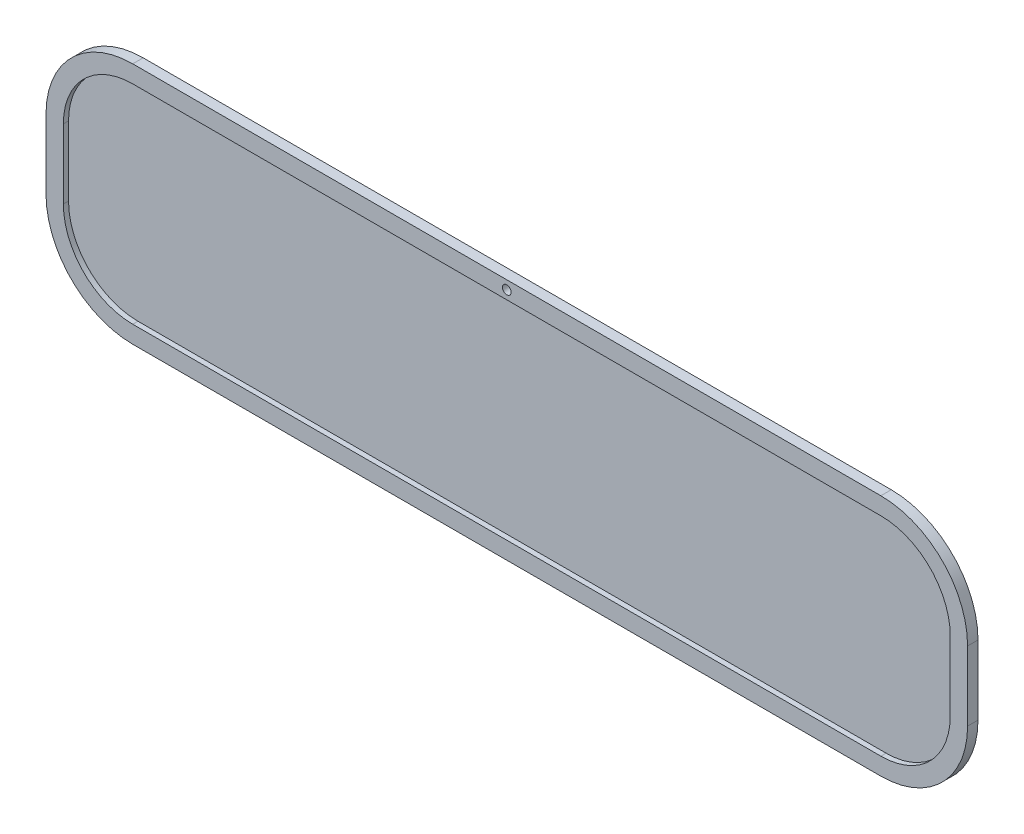
SolidWorks part; units mm, degrees
ref_plane "Ebene vorne" through (0, 0, 0) normal (0, 0, 1) x (1, 0, 0)
ref_plane "Ebene oben" through (0, 0, 0) normal (0, 1, 0) x (1, 0, 0)
ref_plane "Ebene rechts" through (0, 0, 0) normal (1, 0, 0) x (0, 0, -1)
sketch "Skizze1" plane through (0, 0, 0) normal (0, 0, 1) x (1, 0, 0)
  line L8 (432.0512, 126.1723) -> (432.0512, 206.1723)
  line L9 (432.0512, 206.1723) -> (431.4944, 212.0251)
  line L10 (431.4944, 212.0251) -> (429.8454, 217.6528)
  line L11 (429.8454, 217.6528) -> (427.1676, 222.8395)
  line L12 (427.1676, 222.8395) -> (423.5638, 227.3855)
  line L13 (423.5638, 227.3855) -> (419.1726, 231.1164)
  line L14 (419.1726, 231.1164) -> (414.1628, 233.8887)
  line L15 (414.1628, 233.8887) -> (408.7267, 235.5959)
  line L16 (408.7267, 235.5959) -> (403.0734, 236.1723)
  line L17 (403.0734, 236.1723) -> (-70.2302, 236.1723)
  line L18 (-70.2302, 236.1723) -> (-75.8835, 235.5959)
  line L19 (-75.8835, 235.5959) -> (-81.3195, 233.8887)
  line L20 (-81.3195, 233.8887) -> (-86.3294, 231.1164)
  line L21 (-86.3294, 231.1164) -> (-90.7206, 227.3855)
  line L22 (-90.7206, 227.3855) -> (-94.3243, 222.8395)
  line L23 (-94.3243, 222.8395) -> (-97.0022, 217.6528)
  line L24 (-97.0022, 217.6528) -> (-98.6512, 212.0251)
  line L25 (-98.6512, 212.0251) -> (-99.208, 206.1723)
  line L26 (-99.208, 206.1723) -> (-99.208, 126.1723)
  line L27 (-99.208, 126.1723) -> (-98.6512, 120.3196)
  line L28 (-98.6512, 120.3196) -> (-97.0022, 114.6918)
  line L29 (-97.0022, 114.6918) -> (-94.3243, 109.5052)
  line L30 (-94.3243, 109.5052) -> (-90.7206, 104.9591)
  line L31 (-90.7206, 104.9591) -> (-86.3294, 101.2283)
  line L32 (-86.3294, 101.2283) -> (-81.3195, 98.456)
  line L33 (-81.3195, 98.456) -> (-75.8835, 96.7488)
  line L34 (-75.8835, 96.7488) -> (-70.2302, 96.1723)
  line L35 (-70.2302, 96.1723) -> (403.0734, 96.1723)
  line L36 (403.0734, 96.1723) -> (408.7267, 96.7488)
  line L37 (408.7267, 96.7488) -> (414.1628, 98.456)
  line L38 (414.1628, 98.456) -> (419.1726, 101.2283)
  line L39 (419.1726, 101.2283) -> (423.5638, 104.9591)
  line L40 (423.5638, 104.9591) -> (427.1676, 109.5052)
  line L41 (427.1676, 109.5052) -> (429.8454, 114.6918)
  line L42 (429.8454, 114.6918) -> (431.4944, 120.3196)
  line L43 (431.4944, 120.3196) -> (432.0512, 126.1723)
extrude "Aufsatz-Linear austragen1" add sketch "Skizze1" along normal blind 3
sketch "Skizze2" plane through (0, 0, 0) normal (0, 0, -1) x (-1, 0, 0)
  line L0 (-403.0734, 236.1723) -> (70.2302, 236.1723) construction
  line L1 (-379.508, 96.1723) -> (-432.0512, 96.1723)
  line L2 (-379.508, 96.1723) -> (-379.508, 236.1723)
  line L3 (-379.508, 236.1723) -> (-432.0512, 236.1723)
  line L4 (-432.0512, 96.1723) -> (-432.0512, 236.1723)
  line L5 (-432.0512, 126.1723) -> (-432.0512, 206.1723) construction
  line L6 (70.2302, 96.1723) -> (-403.0734, 96.1723) construction
  line L7 (99.208, 206.1723) -> (99.208, 126.1723) construction
  line L8 (-12.0682, 236.1723) -> (99.208, 236.1723)
  line L9 (-12.0682, 236.1723) -> (-12.0682, 96.1723)
  line L10 (-12.0682, 96.1723) -> (99.208, 96.1723)
  line L11 (99.208, 236.1723) -> (99.208, 96.1723)
extrude "Aufsatz-Linear austragen2" add sketch "Skizze2" against normal blind 3
fillet "Verrundung1" radius 50 3 edges at (432.0512, 96.1723, 1.5) (-99.208, 96.1723, 1.5) (-99.208, 236.1723, 1.5)
fillet "Verrundung2" radius 50 1 edges at (432.0512, 236.1723, 1.5)
sketch "Skizze3" plane through (0, 0, 3) normal (0, 0, 1) x (1, 0, 0)
  line L0 (166.4216, 236.1723) -> (166.4216, 96.1723)
  line L1 (382.0512, 236.1723) -> (-49.208, 236.1723) construction
  line L2 (-49.208, 96.1723) -> (382.0512, 96.1723) construction
  circle A0 centre (166.4216, 231.1723) radius 2.5
  dimension "D2" = 5
  dimension "D1" = 5
extrude "Schnitt-Linear austragen1" cut sketch "Skizze3" against normal blind 10 contours A0
sketch "Skizze5" plane through (0, 0, 3) normal (0, 0, 1) x (1, 0, 0)
  line L0 (-89.208, 186.1723) -> (-89.208, 146.1723)
  line L1 (-49.208, 106.1723) -> (382.0512, 106.1723)
  line L2 (422.0512, 146.1723) -> (422.0512, 186.1723)
  line L3 (382.0512, 226.1723) -> (-49.208, 226.1723)
  line L4 (432.0512, 146.1723) -> (432.0512, 186.1723)
  line L5 (382.0512, 236.1723) -> (-49.208, 236.1723)
  line L6 (-99.208, 186.1723) -> (-99.208, 146.1723)
  line L7 (-49.208, 96.1723) -> (382.0512, 96.1723)
  line L8 (432.0512, 146.1723) -> (432.0512, 186.1723)
  line L9 (382.0512, 236.1723) -> (-49.208, 236.1723)
  line L10 (-99.208, 186.1723) -> (-99.208, 146.1723)
  line L11 (-49.208, 96.1723) -> (382.0512, 96.1723)
  arc A0 (-49.208, 226.1723) -> (-89.208, 186.1723) centre (-49.208, 186.1723) ccw
  arc A1 (-89.208, 146.1723) -> (-49.208, 106.1723) centre (-49.208, 146.1723) ccw
  arc A2 (382.0512, 106.1723) -> (422.0512, 146.1723) centre (382.0512, 146.1723) ccw
  arc A3 (422.0512, 186.1723) -> (382.0512, 226.1723) centre (382.0512, 186.1723) ccw
  arc A4 (432.0512, 186.1723) -> (382.0512, 236.1723) centre (382.0512, 186.1723) ccw
  arc A5 (-49.208, 236.1723) -> (-99.208, 186.1723) centre (-49.208, 186.1723) ccw
  arc A6 (-99.208, 146.1723) -> (-49.208, 96.1723) centre (-49.208, 146.1723) ccw
  arc A7 (382.0512, 96.1723) -> (432.0512, 146.1723) centre (382.0512, 146.1723) ccw
  arc A8 (432.0512, 186.1723) -> (382.0512, 236.1723) centre (382.0512, 186.1723) ccw
  arc A9 (-49.208, 236.1723) -> (-99.208, 186.1723) centre (-49.208, 186.1723) ccw
  arc A10 (-99.208, 146.1723) -> (-49.208, 96.1723) centre (-49.208, 146.1723) ccw
  arc A11 (382.0512, 96.1723) -> (432.0512, 146.1723) centre (382.0512, 146.1723) ccw
  dimension "D1" = 0
  dimension "D2" = 10
extrude "Aufsatz-Linear austragen3" add sketch "Skizze5" along normal blind 3
sketch "Skizze6" plane through (0, 0, 0) normal (0, 0, -1) x (-1, 0, 0)
  circle A0 centre (-166.4216, 231.1723) radius 2.5
extrude "Schnitt-Linear austragen2" cut sketch "Skizze6" against normal through all
